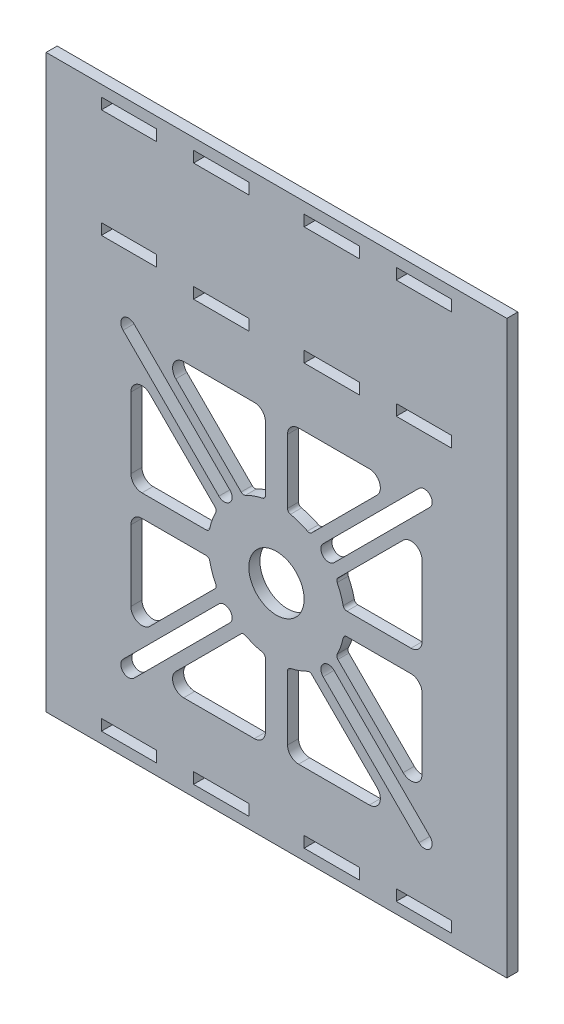
SolidWorks part; units mm, degrees
material "Oak"
ref_plane "Front Plane" through (0, 0, 0) normal (0, 0, 1) x (1, 0, 0)
ref_plane "Top Plane" through (0, 0, 0) normal (0, 1, 0) x (1, 0, 0)
ref_plane "Right Plane" through (0, 0, 0) normal (1, 0, 0) x (0, 0, -1)
sketch "Sketch1" plane through (0, 0, 0) normal (0, 0, 1) x (1, 0, 0)
  line L0 (0, 82.3583) -> (0, -86.853) construction
  line L1 (-62.5, 77.5) -> (62.5, 77.5)
  line L2 (-62.5, 77.5) -> (-62.5, -77.5)
  line L3 (-62.5, -77.5) -> (62.5, -77.5)
  line L4 (62.5, 77.5) -> (62.5, -77.5)
  line L5 (-62.5, 77.5) -> (62.5, -77.5) construction
  line L6 (-62.5, -77.5) -> (62.5, 77.5) construction
  line L7 (-69.8445, 0) -> (74.4392, 0) construction
  line L8 (-74.4542, 74.5) -> (67.0637, 74.5) construction
  line L9 (-74.4542, -74.5) -> (67.0637, -74.5) construction
  line L10 (7.5, 74.5) -> (7.5, 71.5)
  line L11 (-47.5, 74.5) -> (-32.5, 74.5)
  line L12 (-47.5, 74.5) -> (-47.5, 71.5)
  line L13 (-47.5, 71.5) -> (-32.5, 71.5)
  line L14 (-32.5, 74.5) -> (-32.5, 71.5)
  line L15 (-22.5, 74.5) -> (-7.5, 74.5)
  line L16 (-22.5, 74.5) -> (-22.5, 71.5)
  line L17 (-22.5, 71.5) -> (-7.5, 71.5)
  line L18 (-7.5, 74.5) -> (-7.5, 71.5)
  line L19 (22.5, 71.5) -> (7.5, 71.5)
  line L20 (22.5, 74.5) -> (7.5, 74.5)
  line L21 (22.5, 74.5) -> (22.5, 71.5)
  line L22 (32.5, 74.5) -> (32.5, 71.5)
  line L23 (47.5, 71.5) -> (32.5, 71.5)
  line L24 (47.5, 74.5) -> (32.5, 74.5)
  line L25 (47.5, 74.5) -> (47.5, 71.5)
  line L26 (47.5, -74.5) -> (47.5, -71.5)
  line L27 (47.5, -74.5) -> (32.5, -74.5)
  line L28 (47.5, -71.5) -> (32.5, -71.5)
  line L29 (32.5, -74.5) -> (32.5, -71.5)
  line L30 (22.5, -74.5) -> (22.5, -71.5)
  line L31 (22.5, -74.5) -> (7.5, -74.5)
  line L32 (22.5, -71.5) -> (7.5, -71.5)
  line L33 (-7.5, -74.5) -> (-7.5, -71.5)
  line L34 (-22.5, -71.5) -> (-7.5, -71.5)
  line L35 (-22.5, -74.5) -> (-22.5, -71.5)
  line L36 (-22.5, -74.5) -> (-7.5, -74.5)
  line L37 (-32.5, -74.5) -> (-32.5, -71.5)
  line L38 (-47.5, -71.5) -> (-32.5, -71.5)
  line L39 (-47.5, -74.5) -> (-47.5, -71.5)
  line L40 (-47.5, -74.5) -> (-32.5, -74.5)
  line L41 (7.5, -74.5) -> (7.5, -71.5)
  line L42 (-62.5, 41) -> (62.3228, 41) construction
  line L43 (7.5, 42.5) -> (7.5, 39.5)
  line L48 (-7.5, 42.5) -> (-22.5, 42.5)
  line L49 (-7.5, 42.5) -> (-7.5, 39.5)
  line L50 (-7.5, 39.5) -> (-22.5, 39.5)
  line L51 (-22.5, 42.5) -> (-22.5, 39.5)
  line L52 (7.5, 42.5) -> (22.5, 42.5)
  line L53 (7.5, 39.5) -> (22.5, 39.5)
  line L54 (22.5, 42.5) -> (22.5, 39.5)
  line L59 (0, -63.2785) -> (0, 36.7215) construction
  line L60 (-75.2921, -16) -> (68.6825, -16) construction
  line L61 (0, -66.6716) -> (0, 34.6716) construction
  line L62 (39.5, -10) -> (39.5, 9.1863)
  line L63 (0, -16) -> (41.6493, -16) construction
  line L64 (19.0853, -13) -> (36.5, -13)
  line L65 (16.6552, -6.4159) -> (34.3787, 11.3076)
  line L66 (3, -35.0853) -> (3, -52.5)
  line L67 (0, -16) -> (43.1262, 27.1262) construction
  line L68 (6, -55.5) -> (25.1863, -55.5)
  line L69 (9.5841, -32.6552) -> (27.3076, -50.3787)
  line L70 (16.6552, -25.5841) -> (34.3787, -43.3076)
  line L71 (6, 23.5) -> (25.1863, 23.5)
  line L72 (19.0853, -19) -> (36.5, -19)
  line L73 (39.5, -22) -> (39.5, -41.1863)
  line L74 (-3, 3.0853) -> (-3, 20.5)
  line L75 (3, 3.0853) -> (3, 20.5)
  line L76 (9.5841, 0.6552) -> (27.3076, 18.3787)
  line L77 (-6, 23.5) -> (-25.1863, 23.5)
  line L78 (-9.5841, 0.6552) -> (-27.3076, 18.3787)
  line L79 (-39.5, -10) -> (-39.5, 9.1863)
  line L80 (-19.0853, -13) -> (-36.5, -13)
  line L81 (-16.6552, -6.4159) -> (-34.3787, 11.3076)
  line L82 (-19.0853, -19) -> (-36.5, -19)
  line L83 (-16.6552, -25.5841) -> (-34.3787, -43.3076)
  line L84 (-39.5, -22) -> (-39.5, -41.1863)
  line L85 (-3, -35.0853) -> (-3, -52.5)
  line L86 (-9.5841, -32.6552) -> (-27.3076, -50.3787)
  line L87 (-6, -55.5) -> (-25.1863, -55.5)
  line L88 (0, -16) -> (0, -17.5318) construction
  line L89 (0, -16) -> (45.8967, -16) construction
  line L90 (0, -16) -> (50.75, 34.75) construction
  line L91 (14.1421, -1.8579) -> (40.1434, 24.1434) construction
  line L92 (12.6572, -0.3729) -> (38.6585, 25.6283)
  line L93 (15.6271, -3.3428) -> (41.6283, 22.6585)
  line L94 (14.1421, -30.1421) -> (40.1434, -56.1434) construction
  line L95 (12.6572, -31.6271) -> (38.6585, -57.6283)
  line L96 (15.6271, -28.6572) -> (41.6283, -54.6585)
  line L97 (-14.1421, -30.1421) -> (-40.1434, -56.1434) construction
  line L98 (-12.6572, -31.6271) -> (-38.6585, -57.6283)
  line L99 (-15.6271, -28.6572) -> (-41.6283, -54.6585)
  line L100 (-14.1421, -1.8579) -> (-40.1434, 24.1434) construction
  line L101 (-12.6572, -0.3729) -> (-38.6585, 25.6283)
  line L102 (-15.6271, -3.3428) -> (-41.6283, 22.6585)
  line L103 (47.5, 42.5) -> (47.5, 39.5)
  line L104 (47.5, 39.5) -> (32.5, 39.5)
  line L105 (32.5, 39.5) -> (32.5, 42.5)
  line L106 (32.5, 42.5) -> (47.5, 42.5)
  line L108 (-32.5, 45) -> (-32.5, 42)
  line L109 (-32.5, 42) -> (-47.5, 42)
  line L110 (-47.5, 42) -> (-47.5, 45)
  line L111 (-47.5, 45) -> (-32.5, 45)
  circle A0 centre (0, -16) radius 7.5
  arc A1 (3.7949, -34.1066) -> (3, -35.0853) centre (4, -35.0853) ccw
  arc A2 (8.4218, 0.4719) -> (3.7949, 2.1066) centre (0, -16) ccw
  arc A3 (8.4218, -32.4719) -> (3.7949, -34.1066) centre (0, -16) cw
  arc A4 (27.3076, 18.3787) -> (25.1863, 23.5) centre (25.1863, 20.5) ccw
  arc A5 (3, 20.5) -> (6, 23.5) centre (6, 20.5) cw
  arc A6 (9.5841, 0.6552) -> (8.4218, 0.4719) centre (8.877, 1.3623) cw
  arc A7 (3.7949, 2.1066) -> (3, 3.0853) centre (4, 3.0853) cw
  arc A8 (36.5, -13) -> (39.5, -10) centre (36.5, -10) ccw
  arc A9 (18.1066, -12.2051) -> (19.0853, -13) centre (19.0853, -12) ccw
  arc A10 (16.4719, -7.5782) -> (18.1066, -12.2051) centre (0, -16) cw
  arc A11 (16.6552, -6.4159) -> (16.4719, -7.5782) centre (17.3623, -7.123) ccw
  arc A12 (34.3787, 11.3076) -> (39.5, 9.1863) centre (36.5, 9.1863) cw
  arc A13 (9.5841, -32.6552) -> (8.4218, -32.4719) centre (8.877, -33.3623) ccw
  arc A14 (3, -52.5) -> (6, -55.5) centre (6, -52.5) ccw
  arc A15 (27.3076, -50.3787) -> (25.1863, -55.5) centre (25.1863, -52.5) cw
  arc A16 (16.6552, -25.5841) -> (16.4719, -24.4218) centre (17.3623, -24.877) cw
  arc A17 (16.4719, -24.4218) -> (18.1066, -19.7949) centre (0, -16) ccw
  arc A18 (18.1066, -19.7949) -> (19.0853, -19) centre (19.0853, -20) cw
  arc A19 (36.5, -19) -> (39.5, -22) centre (36.5, -22) cw
  arc A20 (34.3787, -43.3076) -> (39.5, -41.1863) centre (36.5, -41.1863) ccw
  arc A21 (-3.7949, 2.1066) -> (-3, 3.0853) centre (-4, 3.0853) ccw
  arc A22 (-8.4218, 0.4719) -> (-3.7949, 2.1066) centre (0, -16) cw
  arc A23 (-9.5841, 0.6552) -> (-8.4218, 0.4719) centre (-8.877, 1.3623) ccw
  arc A24 (-3, 20.5) -> (-6, 23.5) centre (-6, 20.5) ccw
  arc A25 (-27.3076, 18.3787) -> (-25.1863, 23.5) centre (-25.1863, 20.5) cw
  arc A26 (-34.3787, 11.3076) -> (-39.5, 9.1863) centre (-36.5, 9.1863) ccw
  arc A27 (-36.5, -13) -> (-39.5, -10) centre (-36.5, -10) cw
  arc A28 (-18.1066, -12.2051) -> (-19.0853, -13) centre (-19.0853, -12) cw
  arc A29 (-16.6552, -6.4159) -> (-16.4719, -7.5782) centre (-17.3623, -7.123) cw
  arc A30 (-16.4719, -7.5782) -> (-18.1066, -12.2051) centre (0, -16) ccw
  arc A31 (-16.6552, -25.5841) -> (-16.4719, -24.4218) centre (-17.3623, -24.877) ccw
  arc A32 (-16.4719, -24.4218) -> (-18.1066, -19.7949) centre (0, -16) cw
  arc A33 (-18.1066, -19.7949) -> (-19.0853, -19) centre (-19.0853, -20) ccw
  arc A34 (-36.5, -19) -> (-39.5, -22) centre (-36.5, -22) ccw
  arc A35 (-34.3787, -43.3076) -> (-39.5, -41.1863) centre (-36.5, -41.1863) cw
  arc A36 (-9.5841, -32.6552) -> (-8.4218, -32.4719) centre (-8.877, -33.3623) cw
  arc A37 (-8.4218, -32.4719) -> (-3.7949, -34.1066) centre (0, -16) ccw
  arc A38 (-3.7949, -34.1066) -> (-3, -35.0853) centre (-4, -35.0853) cw
  arc A39 (-3, -52.5) -> (-6, -55.5) centre (-6, -52.5) cw
  arc A40 (-27.3076, -50.3787) -> (-25.1863, -55.5) centre (-25.1863, -52.5) ccw
  arc A41 (12.6572, -0.3729) -> (15.6271, -3.3428) centre (14.1421, -1.8579) ccw
  arc A42 (41.6283, 22.6585) -> (38.6585, 25.6283) centre (40.1434, 24.1434) ccw
  arc A43 (12.6572, -31.6271) -> (15.6271, -28.6572) centre (14.1421, -30.1421) cw
  arc A44 (41.6283, -54.6585) -> (38.6585, -57.6283) centre (40.1434, -56.1434) cw
  arc A45 (-12.6572, -31.6271) -> (-15.6271, -28.6572) centre (-14.1421, -30.1421) ccw
  arc A46 (-41.6283, -54.6585) -> (-38.6585, -57.6283) centre (-40.1434, -56.1434) ccw
  arc A47 (-12.6572, -0.3729) -> (-15.6271, -3.3428) centre (-14.1421, -1.8579) cw
  arc A48 (-41.6283, 22.6585) -> (-38.6585, 25.6283) centre (-40.1434, 24.1434) cw
  point P0 (0, 0)
  point P64 (0, -16)
  point P65 (-7.5, 41)
  point P176 (0, -16)
  point P180 (27.1428, 11.1428)
  point P187 (27.1428, -43.1428)
  point P194 (-27.1428, -43.1428)
  point P201 (-27.1428, 11.1428)
  point P209 (47.5, -73)
  dimension "D1" = 125
  dimension "D2" = 155
  dimension "D3" = 3
  dimension "D4" = 15
  dimension "D5" = 15
  dimension "D6" = 3
  dimension "D7" = 10
  dimension "D8" = 15
  dimension "D9" = 3
  dimension "D10" = 7.5
  dimension "D11" = 118.5
  dimension "D12" = 3
  dimension "D13" = 15
  dimension "D14" = 15
  dimension "D15" = 15
  dimension "D17" = 3
  dimension "D18" = 1.5
  dimension "D19" = 55.5
  dimension "D20" = 15
  dimension "D21" = 10
  dimension "D22" = 7.5
  dimension "D23" = 7.5
  dimension "D25" = 15
  dimension "D26" = 3
  dimension "D27" = 155
  dimension "D28" = 15
  dimension "D29" = 1.5
  dimension "D30" = 1.5
extrude "Boss-Extrude1" add sketch "Sketch1" along normal blind 3
